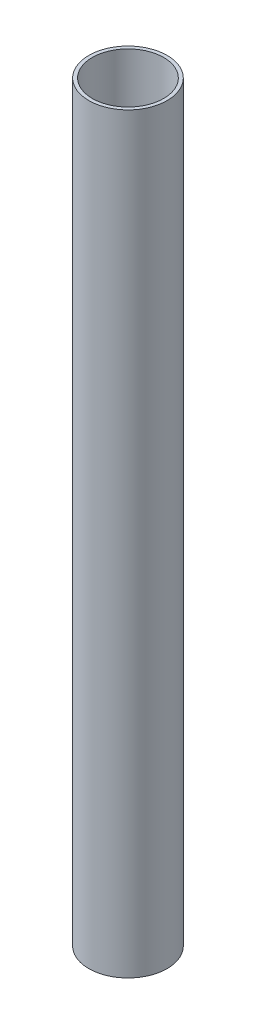
SolidWorks part; units mm, degrees
ref_plane "Front Plane" through (0, 0, 0) normal (0, 0, 1) x (1, 0, 0)
ref_plane "Top Plane" through (0, 0, 0) normal (0, 1, 0) x (1, 0, 0)
ref_plane "Right Plane" through (0, 0, 0) normal (1, 0, 0) x (0, 0, -1)
sketch "Sketch1" plane through (0, 0, 0) normal (0, 1, 0) x (1, 0, 0)
  circle A0 centre (0, 0) radius 7.9375
  circle A1 centre (0, 0) radius 7.2263
  dimension "D1" = 15.875
  dimension "D2" = 14.4526
extrude "Boss-Extrude1" add sketch "Sketch1" along normal blind 152.4
